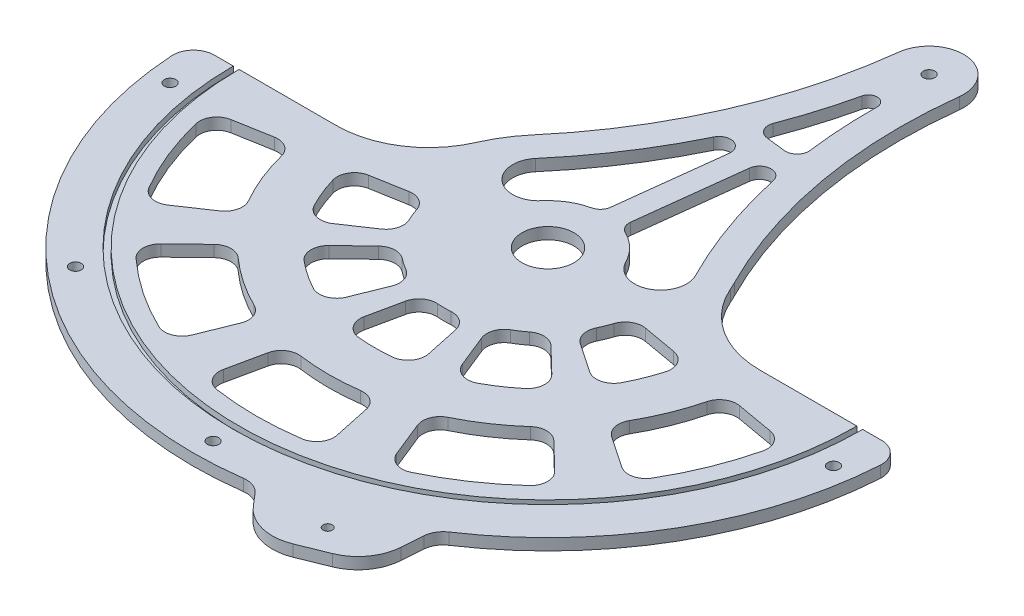
SolidWorks part; units mm, degrees
material "Polycarbonate"
ref_plane "Front Plane" through (0, 0, 0) normal (0, 0, 1) x (1, 0, 0)
ref_plane "Top Plane" through (0, 0, 0) normal (0, 1, 0) x (1, 0, 0)
ref_plane "Right Plane" through (0, 0, 0) normal (1, 0, 0) x (0, 0, -1)
sketch "Sketch1" plane through (0, 0, 0) normal (0, 1, 0) x (1, 0, 0)
  line L0 (76.2, 0) -> (173.0375, 0)
  line L3 (-173.0375, 0) -> (-76.2, 0)
  arc A0 (-169.8625, 0) -> (169.8625, 0) centre (0, 0) ccw construction
  arc A1 (173.0375, 0) -> (-173.0375, 0) centre (0, 0) cw
  arc A2 (-76.2, 0) -> (76.2, 0) centre (0, 0) cw
  dimension "D1" = 169.8625
  dimension "D2" = 3.175
  dimension "D4" = 76.2
extrude "Boss-Extrude1" add sketch "Sketch1" along normal mid plane 6.35
sketch "Sketch2" plane through (0, 3.175, 0) normal (0, 1, 0) x (1, 0, 0)
  line L0 (-76.2, 0) -> (-173.0375, 0) construction
  line L1 (173.0375, 0) -> (76.2, 0) construction
  line L2 (0, 0) -> (0, 34.6103) construction
  line L3 (-78.9658, -53.2631) -> (-47.3795, -31.9579)
  line L4 (-56.2818, -9.924) -> (-93.8029, -16.54)
  line L5 (-60.0635, -148.6623) -> (-45.1963, -111.8647)
  line L6 (-157.9016, -27.8423) -> (-132.9258, -89.6596) construction
  line L7 (-86.7883, -83.8105) -> (-115.3371, -111.3798)
  line L8 (-35.6813, -88.3143) -> (-21.4088, -52.9886)
  line L9 (-41.1103, -39.6997) -> (-68.5171, -66.1662)
  line L10 (-132.9258, -89.6596) -> (-100.0234, -67.4666)
  line L11 (-118.8171, -20.9507) -> (-157.9016, -27.8423)
  line L12 (33.336, -156.8337) -> (25.0845, -118.0135)
  line L13 (-118.8171, -20.9507) -> (-100.0234, -67.4666) construction
  line L14 (-25.0845, -118.0135) -> (-33.336, -156.8337)
  line L15 (19.8036, -93.1686) -> (11.8822, -55.9011)
  line L16 (-11.8822, -55.9011) -> (-19.8036, -93.1686)
  line L17 (115.3371, -111.3798) -> (86.7883, -83.8105)
  line L18 (45.1963, -111.8647) -> (60.0635, -148.6623)
  line L19 (68.5171, -66.1662) -> (41.1103, -39.6997)
  line L20 (21.4088, -52.9886) -> (35.6813, -88.3143)
  line L21 (157.9016, -27.8423) -> (118.8171, -20.9507)
  line L22 (100.0234, -67.4666) -> (132.9258, -89.6596)
  line L23 (93.8029, -16.54) -> (56.2818, -9.924)
  line L24 (47.3795, -31.9579) -> (78.9658, -53.2631)
  line L27 (0, 0) -> (-38.1044, -101.0013) construction
  line L28 (-88.3143, -35.6813) -> (-111.8647, -45.1963) construction
  arc A0 (-157.9016, -27.8423) -> (-132.9258, -89.6596) centre (0, 0) ccw
  arc A1 (-93.8029, -16.54) -> (-78.9658, -53.2631) centre (0, 0) ccw
  arc A2 (-56.2818, -9.924) -> (-47.3795, -31.9579) centre (0, 0) ccw
  arc A3 (-86.7883, -83.8105) -> (-45.1963, -111.8647) centre (0, 0) ccw
  arc A4 (-173.0375, 0) -> (173.0375, 0) centre (0, 0) ccw construction
  arc A5 (-118.8171, -20.9507) -> (-100.0234, -67.4666) centre (0, 0) ccw
  arc A6 (-115.3371, -111.3798) -> (-60.0635, -148.6623) centre (0, 0) ccw
  arc A7 (-68.5171, -66.1662) -> (-35.6813, -88.3143) centre (0, 0) ccw
  arc A8 (-41.1103, -39.6997) -> (-21.4088, -52.9886) centre (0, 0) ccw
  arc A9 (-25.0845, -118.0135) -> (25.0845, -118.0135) centre (0, 0) ccw
  arc A10 (-33.336, -156.8337) -> (33.336, -156.8337) centre (0, 0) ccw
  arc A11 (-19.8036, -93.1686) -> (19.8036, -93.1686) centre (0, 0) ccw
  arc A12 (-11.8822, -55.9011) -> (11.8822, -55.9011) centre (0, 0) ccw
  arc A13 (45.1963, -111.8647) -> (86.7883, -83.8105) centre (0, 0) ccw
  arc A14 (60.0635, -148.6623) -> (115.3371, -111.3798) centre (0, 0) ccw
  arc A15 (35.6813, -88.3143) -> (68.5171, -66.1662) centre (0, 0) ccw
  arc A16 (21.4088, -52.9886) -> (41.1103, -39.6997) centre (0, 0) ccw
  arc A17 (100.0234, -67.4666) -> (118.8171, -20.9507) centre (0, 0) ccw
  arc A18 (132.9258, -89.6596) -> (157.9016, -27.8423) centre (0, 0) ccw
  arc A19 (78.9658, -53.2631) -> (93.8029, -16.54) centre (0, 0) ccw
  arc A20 (47.3795, -31.9579) -> (56.2818, -9.924) centre (0, 0) ccw
  circle A22 centre (0, 0) radius 107.95 construction
  circle A23 centre (0, 0) radius 50.8 construction
  circle A24 centre (-38.1044, -101.0013) radius 61.9125 construction
  circle A25 centre (-17.0909, -45.302) radius 2.3812 construction
  point P51 (0, 0)
  point P54 (0, 0)
  point P65 (-100.0895, -40.4388)
  dimension "D1" = 12.7
  dimension "D2" = 101.6
  dimension "D3" = 10
  dimension "D5" = 25.4
  dimension "D6" = 57.15
  dimension "D4" = 123.825
  dimension "D8" = 4.7625
  dimension "D9" = 10
  dimension "D10" = 10
  dimension "D7" = 5
extrude "Cut-Extrude1" cut sketch "Sketch2" against normal through all
sketch "Sketch4" plane through (0, 0, 0) normal (0, 1, 0) x (1, 0, 0)
  line L0 (173.0375, 0) -> (195.2625, 0)
  line L4 (-195.2625, 0) -> (-173.0375, 0)
  arc A0 (-195.2625, 0) -> (195.2625, 0) centre (0, 0) ccw
  arc A1 (-173.0375, 0) -> (173.0375, 0) centre (0, 0) ccw construction
  arc A2 (-173.0375, 0) -> (173.0375, 0) centre (0, 0) ccw
  dimension "D1" = 22.225
sketch "Sketch5" plane through (0, 3.175, 0) normal (0, 1, 0) x (1, 0, 0)
  line L0 (-76.2, 0) -> (-173.0375, 0) construction
  line L1 (169.8625, 0) -> (173.0375, 0)
  line L6 (-169.8625, 0) -> (-173.0375, 0)
  arc A0 (-169.8625, 0) -> (169.8625, 0) centre (0, 0) ccw
  arc A1 (-173.0375, 0) -> (173.0375, 0) centre (0, 0) ccw construction
  arc A2 (-173.0375, 0) -> (173.0375, 0) centre (0, 0) ccw
  dimension "D1" = 3.175
extrude "Cut-Extrude2" cut sketch "Sketch5" against normal blind 3.175
extrude "Boss-Extrude2" add sketch "Sketch4" against normal mid plane 6.35 contours A0 L0 A2 L4
sketch "Sketch6" plane through (0, 3.175, 0) normal (0, 1, 0) x (1, 0, 0)
  circle A0 centre (0, 0) radius 14.2875
  dimension "D1" = 28.575
extrude "Cut-Extrude3" cut sketch "Sketch6" against normal through all
sketch "Sketch7" plane through (0, 3.175, 0) normal (0, 1, 0) x (1, 0, 0)
  line L0 (32.2069, -192.5881) -> (53.9687, -217.9881)
  line L1 (53.9687, -217.9881) -> (101.0697, -198.958)
  line L2 (101.0697, -198.958) -> (103.4662, -165.5965)
  line L4 (32.2069, -192.5881) -> (103.4662, -165.5965)
  arc A0 (-195.2625, 0) -> (195.2625, 0) centre (0, 0) ccw construction
  arc A2 (-195.2625, 0) -> (195.2625, 0) centre (0, 0) ccw construction
extrude "Boss-Extrude3" add sketch "Sketch7" against normal through all contours L4 L2 L1 L0
sketch "Sketch8" plane through (0, 3.175, 0) normal (0, 1, 0) x (-1, 0, 0)
  line L1 (-67.8365, 179.0923) -> (-77.5192, 208.4731) construction
  line L2 (-53.9687, 217.9881) -> (-101.0697, 198.958) construction
  line L3 (-32.2069, 192.5881) -> (-67.8365, 179.0923) construction
  line L4 (-67.8365, 179.0923) -> (-103.4662, 165.5965) construction
  circle A0 centre (-72.6779, 193.7827) radius 2.54
  point P8 (-72.6779, 193.7827)
  point P14 (-77.5192, 208.4731)
  dimension "D1" = 5.08
extrude "Cut-Extrude4" cut sketch "Sketch8" against normal through all
sketch "Sketch9" plane through (0, 3.175, 0) normal (0, 1, 0) x (1, 0, 0)
  line L0 (-184.15, 0) -> (-173.0375, 0) construction
  line L1 (-195.2625, 0) -> (-173.0375, 0) construction
  line L2 (-184.15, 0) -> (-195.2625, 0) construction
  line L3 (182.3899, -25.4) -> (184.15, 0) construction
  line L4 (-184.15, 0) -> (-182.3899, -25.4) construction
  line L5 (182.3899, -25.4) -> (120.9004, -138.904) construction
  line L6 (120.9004, -138.904) -> (0, -184.15) construction
  line L7 (0, -184.15) -> (-120.9004, -138.904) construction
  line L8 (-120.9004, -138.904) -> (-182.3899, -25.4) construction
  circle A0 centre (-182.3899, -25.4) radius 3.175
  circle A1 centre (-120.9004, -138.904) radius 3.175
  circle A2 centre (0, -184.15) radius 3.175
  circle A3 centre (120.9004, -138.904) radius 3.175 construction
  circle A4 centre (182.3899, -25.4) radius 3.175
  circle A5 centre (0, 0) radius 184.15 construction
  circle A6 centre (0, 0) radius 173.0375 construction
  dimension "D1" = 6.35
  dimension "D2" = 25.4
extrude "Cut-Extrude5" cut sketch "Sketch9" against normal through all
fillet "Fillet1" radius 25.4 2 edges at (101.0697, 0, 198.958) (53.9687, 0, 217.9881)
fillet "Fillet2" radius 9.525 40 edges at (-93.8029, 0, 16.54) (-78.9658, 0, 53.2631) (-47.3795, 0, 31.9579) (-56.2818, 0, 9.924) (-118.8171, 0, 20.9507) (157.9016, 0, 27.8423) (132.9258, 0, 89.6596) (118.8171, 0, 20.9507) (100.0234, 0, 67.4666) (47.3795, 0, 31.9579) (78.9658, 0, 53.2631) (93.8029, 0, 16.54) (56.2818, 0, 9.924) (86.7883, 0, 83.8105) (115.3371, 0, 111.3798) (60.0635, 0, 148.6623) (45.1963, 0, 111.8647) (68.5171, 0, 66.1662) (21.4088, 0, 52.9886) (35.6813, 0, 88.3143) (41.1103, 0, 39.6997) (-19.8036, 0, 93.1686) (19.8036, 0, 93.1686) (11.8822, 0, 55.9011) (-11.8822, 0, 55.9011) (25.0845, 0, 118.0135) (33.336, 0, 156.8337) (-33.336, 0, 156.8337) (-25.0845, 0, 118.0135) (-21.4088, 0, 52.9886) (-35.6813, 0, 88.3143) (-68.5171, 0, 66.1662) (-41.1103, 0, 39.6997) (-115.3371, 0, 111.3798) (-60.0635, 0, 148.6623) (-86.7883, 0, 83.8105) (-157.9016, 0, 27.8423) (-132.9258, 0, 89.6596) (-45.1963, 0, 111.8647) (-100.0234, 0, 67.4666)
fillet "Fillet4" radius 11.43 4 edges at (32.2069, 0, 192.5881) (103.4662, 0, 165.5965) (195.2625, 0, 0) (-195.2625, 0, 0)
fillet "Fillet3" radius 50.8 2 edges at (76.2, 0, 0) (-76.2, 0, 0)
sketch "Sketch10" plane through (0, 3.175, 0) normal (0, 1, 0) x (1, 0, 0)
  line L0 (41.1423, 185.0806) -> (3.3077, 189.5694) construction
  arc A0 (67.9289, 34.5268) -> (-57.964, 49.4632) centre (0, 0) ccw
  arc A1 (3.3077, 189.5694) -> (41.1423, 185.0806) centre (22.225, 187.325) cw
  arc A2 (41.1423, 185.0806) -> (67.9289, 34.5268) centre (303.0074, 154.0119) ccw
  arc A3 (69.8385, 30.48) -> (-69.8385, 30.48) centre (0, 0) ccw construction
  arc A4 (3.3077, 189.5694) -> (-57.964, 49.4632) centre (-258.5574, 220.6382) cw
  circle A5 centre (22.225, 187.325) radius 3.175
  dimension "D1" = 19.05
  dimension "D3" = 6.35
  dimension "D2" = 38.1
  dimension "D4" = 187.325
  dimension "D5" = 22.225
extrude "Boss-Extrude4" add sketch "Sketch10" against normal through all contours A2 L0 A5 A4 A0 | L0 A1 A5
sketch "Sketch11" [suppressed] plane through (0, 3.175, 0) normal (0, 1, 0) x (1, 0, 0)
  line L0 (-179.3875, 0) -> (-195.2892, 0)
  line L1 (-87.9882, 0) -> (-192.0613, 0) construction
  line L2 (-195.2892, 0) -> (-195.2358, -3.2275)
  line L3 (179.3875, 0) -> (195.2892, 0)
  line L4 (192.0613, 0) -> (87.9882, 0) construction
  line L5 (195.2892, 0) -> (195.2358, -3.2275)
  line L7 (33.3672, -193.9423) -> (22.1072, -180.8)
  line L8 (33.3672, -193.9423) -> (42.0912, -204.1249) construction
  line L9 (103.3511, -167.1982) -> (104.6985, -148.4419)
  line L10 (102.2045, -183.1606) -> (103.3511, -167.1982) construction
  arc A0 (-195.2358, -3.2275) -> (30.4608, -192.8719) centre (0, 0) ccw construction
  arc A1 (-195.2358, -3.2275) -> (30.4608, -192.8719) centre (0, 0) ccw
  arc A2 (104.8137, -164.7469) -> (195.2358, -3.2275) centre (0, 0) ccw construction
  arc A3 (104.8137, -164.7469) -> (195.2358, -3.2275) centre (0, 0) ccw
  arc A4 (-179.3875, 0) -> (16.6941, -178.609) centre (0, 0) ccw
  arc A5 (179.3875, 0) -> (107.2362, -143.8064) centre (0, 0) cw
  arc A6 (33.3672, -193.9423) -> (30.4608, -192.8719) centre (30.9561, -196.0081) ccw construction
  arc A7 (33.3672, -193.9423) -> (30.4608, -192.8719) centre (30.9561, -196.0081) ccw
  arc A8 (104.8137, -164.7469) -> (103.3511, -167.1982) centre (106.518, -167.4257) ccw construction
  arc A9 (104.8137, -164.7469) -> (103.3511, -167.1982) centre (106.518, -167.4257) ccw
  arc A10 (107.2362, -143.8064) -> (104.6985, -148.4419) centre (111.0322, -148.8969) ccw
  arc A11 (16.6941, -178.609) -> (22.1072, -180.8) centre (17.2851, -184.9315) cw
  dimension "D1" = 15.875
  dimension "D2" = 6.35
extrude "Cut-Extrude7" [suppressed] cut sketch "Sketch11" against normal through all
sketch "Sketch12" plane through (0, 3.175, 0) normal (0, 1, 0) x (1, 0, 0)
  line L0 (0, 0) -> (6.4672, 54.5092) construction
  line L1 (-2.0736, 36.419) -> (4.8505, 94.7799)
  line L2 (10.5379, 34.9227) -> (17.4621, 93.2836)
  line L3 (-35.0199, 29.884) -> (41.0404, 20.8599) construction
  line L4 (7.8852, 112.5328) -> (18.6657, 111.2538)
  line L5 (8.6334, 118.8386) -> (-1.4552, 95.5281) construction
  arc A0 (17.4621, 93.2836) -> (29.9693, 93.9008) centre (23.7679, 92.5355) cw
  arc A1 (14.0463, 158.5868) -> (2.6995, 121.0994) centre (-258.5574, 220.6382) cw
  arc A2 (23.4521, 157.4709) -> (25.712, 118.3691) centre (303.0074, 154.0119) ccw
  arc A3 (14.0463, 158.5868) -> (23.4521, 157.4709) centre (18.69, 157.5298) cw
  arc A4 (2.6995, 121.0994) -> (7.8852, 112.5328) centre (8.6334, 118.8386) ccw
  arc A5 (18.6657, 111.2538) -> (25.712, 118.3691) centre (19.4139, 117.5595) ccw
  arc A10 (-45.8882, 39.1584) -> (-55.2888, 24.13) centre (0, 0) ccw
  arc A11 (-45.8882, 39.1584) -> (19.0721, 187.6991) centre (-258.5574, 220.6382) ccw
  arc A12 (-24.1517, 20.6097) -> (-6.9828, 30.9726) centre (0, 0) cw
  arc A13 (-45.8882, 39.1584) -> (-7.1651, 98.3066) centre (-258.5574, 220.6382) ccw
  circle A14 centre (0, 0) radius 31.75 construction
  arc A15 (-45.8882, 39.1584) -> (-24.1517, 20.6097) centre (-35.0199, 29.884) ccw
  arc A16 (55.2888, 24.13) -> (53.7771, 27.3337) centre (0, 0) ccw
  arc A17 (25.3779, 186.9509) -> (53.7771, 27.3337) centre (303.0074, 154.0119) ccw
  arc A18 (-6.9828, 30.9726) -> (-2.0736, 36.419) centre (-8.3794, 37.1671) ccw
  arc A19 (29.9693, 93.9008) -> (53.7771, 27.3337) centre (303.0074, 154.0119) ccw
  arc A20 (53.7771, 27.3337) -> (28.3037, 14.3862) centre (41.0404, 20.8599) cw
  arc A21 (28.3037, 14.3862) -> (14.0364, 28.4788) centre (0, 0) ccw
  arc A22 (14.0364, 28.4788) -> (10.5379, 34.9227) centre (16.8437, 34.1746) cw
  arc A23 (4.8505, 94.7799) -> (-7.1651, 98.3066) centre (-1.4552, 95.5281) ccw
  point P27 (3.0102, 25.372)
  point P42 (6.1112, 113.011)
  point P43 (1.0669, 101.3557)
  dimension "D3" = 63.5
  dimension "D4" = 12.7
  dimension "D5" = 6.35
  dimension "D6" = 6.35
  dimension "D7" = 4.7625
  dimension "D8" = 6.35
  dimension "D9" = 12.7
  dimension "D1" = 15.875
  dimension "D2" = 15.875
extrude "Cut-Extrude8" cut sketch "Sketch12" against normal through all
